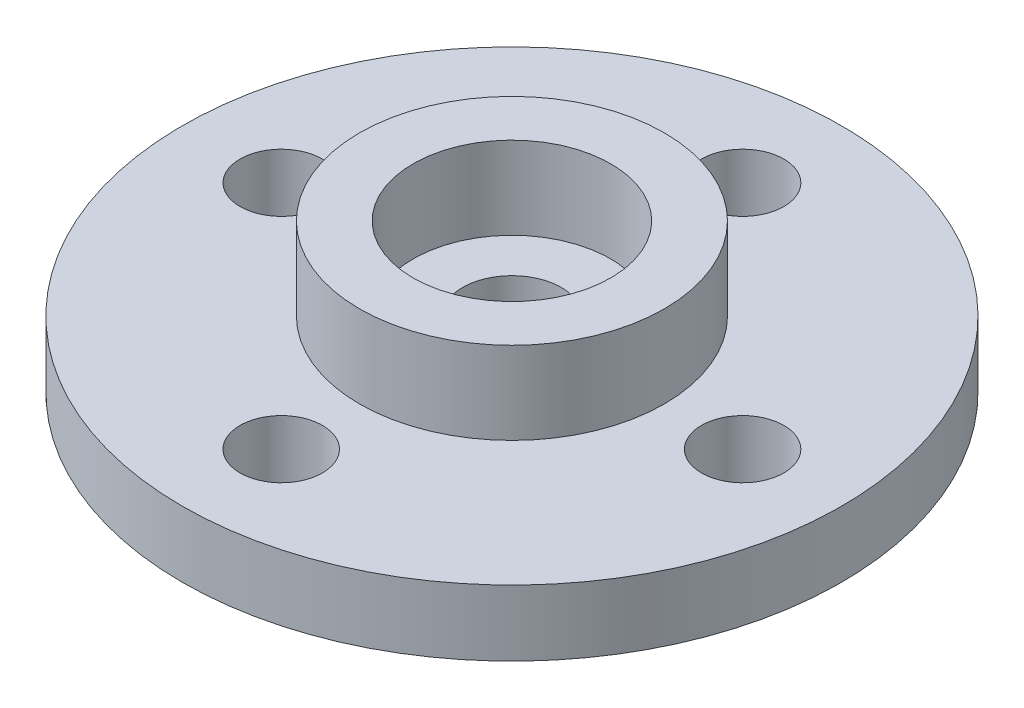
SolidWorks part; units mm, degrees
ref_plane "Front Plane" through (0, 0, 0) normal (0, 0, 1) x (1, 0, 0)
ref_plane "Top Plane" through (0, 0, 0) normal (0, 1, 0) x (1, 0, 0)
ref_plane "Right Plane" through (0, 0, 0) normal (1, 0, 0) x (0, 0, -1)
sketch "Sketch1" plane through (0, 0, 0) normal (0, 1, 0) x (1, 0, 0)
  circle A0 centre (0, 0) radius 10
  circle A1 centre (0, 7) radius 1.25
  circle A2 centre (0, 0) radius 1.5
  circle A3 centre (7, 0) radius 1.25
  circle A4 centre (0, -7) radius 1.25
  circle A5 centre (-7, 0) radius 1.25
  point P15 (0, 0)
  dimension "D1" = 20
  dimension "D2" = 7
  dimension "D3" = 2.5
  dimension "D4" = 3
  dimension "D5" = 4
extrude "Boss-Extrude1" add sketch "Sketch1" along normal blind 2
sketch "Sketch2" plane through (0, 2, 0) normal (0, 1, 0) x (1, 0, 0)
  circle A0 centre (0, 0) radius 4.625
  circle A1 centre (0, 0) radius 3
  dimension "D1" = 9.25
  dimension "D2" = 6
extrude "Boss-Extrude2" add sketch "Sketch2" along normal blind 2.5
